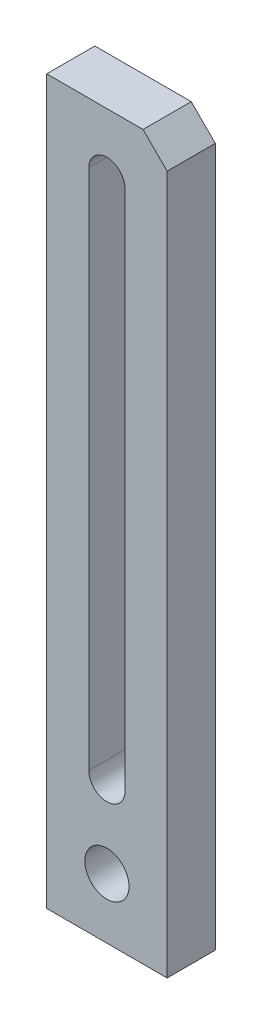
SolidWorks part; units mm, degrees
ref_plane "前视基准面" through (0, 0, 0) normal (0, 0, 1) x (1, 0, 0)
ref_plane "上视基准面" through (0, 0, 0) normal (0, 1, 0) x (1, 0, 0)
ref_plane "右视基准面" through (0, 0, 0) normal (1, 0, 0) x (0, 0, -1)
sketch "草图1" plane through (0, 0, 0) normal (0, 0, 1) x (1, 0, 0)
  line L1 (-15, 90) -> (15, 90)
  line L2 (-15, 90) -> (-15, -90)
  line L3 (-15, -90) -> (15, -90)
  line L4 (15, 90) -> (15, -90)
  line L5 (-15, 90) -> (15, -90) construction
  line L6 (-15, -90) -> (15, 90) construction
  point P0 (0, 0)
  dimension "D1" = 30
  dimension "D2" = 180
extrude "凸台-拉伸1" add sketch "草图1" along normal blind 12
sketch "草图2" plane through (0, 0, 12) normal (0, 0, 1) x (1, 0, 0)
  line L0 (0, 75) -> (0, -55) construction
  line L1 (4.5, 75) -> (4.5, -55)
  line L2 (-4.5, 75) -> (-4.5, -55)
  line L3 (-15, -90) -> (15, -90) construction
  line L4 (-15, 90) -> (-15, -90) construction
  arc A0 (4.5, 75) -> (-4.5, 75) centre (0, 75) ccw
  arc A1 (-4.5, -55) -> (4.5, -55) centre (0, -55) ccw
  circle A2 centre (0, -75) radius 5.5
  point P3 (0, 10)
  dimension "D4" = 11
  dimension "D1" = 9
  dimension "D2" = 130
  dimension "D3" = 20
  dimension "D5" = 15
  dimension "D6" = 15
extrude "切除-拉伸1" cut sketch "草图2" against normal blind 12
chamfer "倒角1" distance 6 angle 45 1 edges at (15, 90, 6)
